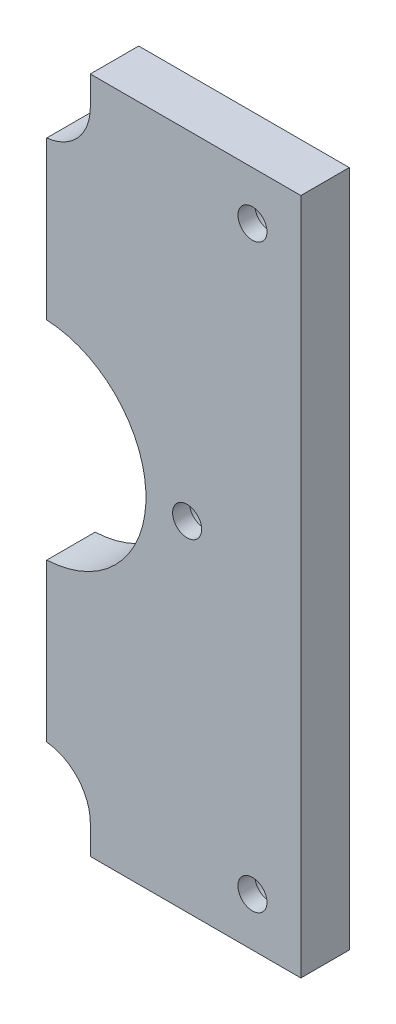
SolidWorks part; units mm, degrees
material "7079 Alloy"
ref_plane "Front" through (0, 0, 0) normal (0, 0, 1) x (1, 0, 0)
ref_plane "Top" through (0, 0, 0) normal (0, 1, 0) x (1, 0, 0)
ref_plane "Right" through (0, 0, 0) normal (1, 0, 0) x (0, 0, -1)
sketch "Sketch1" plane through (0, 0, 0) normal (0, 0, 1) x (1, 0, 0)
  line L0 (26.5, 140) -> (20.5, 140)
  line L1 (20.5, 0) -> (26.5, 0)
  line L2 (5.5, 100) -> (20.5, 100)
  line L3 (26.5, 6) -> (26.5, 0)
  line L4 (90, 0) -> (90, 140)
  line L5 (5.5, 40) -> (20.5, 40)
  line L6 (37.4999, 100) -> (37.4999, 91.4767)
  line L7 (26.5, 140) -> (26.5, 134)
  line L8 (35.5, 100) -> (35.5, 91.4767)
  line L9 (5.5, 100) -> (0, 100)
  line L10 (35.5, 40) -> (35.5, 48.5233)
  line L11 (20.5, 40) -> (20.5, 0)
  line L12 (20.5, 100) -> (20.5, 140)
  line L13 (0, 140) -> (0, 0) construction
  line L14 (37.4999, 48.5233) -> (37.4999, 39.9891)
  line L15 (46.5, 0) -> (46.5, 6)
  line L16 (46.5, 140) -> (90, 140)
  line L17 (37.4999, 15.9499) -> (37.4999, 39.9891)
  line L18 (46.5, 140) -> (46.5, 134)
  line L19 (37.4999, 100) -> (37.4999, 124.0501)
  line L20 (0, 140) -> (26.5, 140) construction
  line L21 (46.5, 0) -> (90, 0)
  line L22 (0, 100) -> (0, 40)
  line L23 (35.5, 124.0501) -> (35.5, 100)
  line L24 (35.5, 40) -> (35.5, 15.9499)
  line L25 (0, 40) -> (5.5, 40)
  arc A0 (35.5, 91.4767) -> (35.5, 48.5233) centre (36.5, 70) ccw
  circle A1 centre (80, 10) radius 3
  circle A2 centre (66.5, 70) radius 3
  circle A3 centre (80, 130) radius 3
  arc A4 (37.4999, 48.5233) -> (37.4999, 91.4767) centre (36.5, 70) ccw
  arc A5 (35.5, 15.9499) -> (26.5, 6) centre (36.5, 6) ccw
  arc A6 (26.5, 134) -> (46.5, 134) centre (36.5, 134) ccw
  arc A7 (46.5, 6) -> (37.4999, 15.9499) centre (36.5, 6) ccw
  circle A8 centre (6.5, 70) radius 3
  dimension "D1" = 140
extrude "Extrude2" add sketch "Sketch1" along normal blind 10
sketch "Sketch5" plane through (0, 0, 0) normal (0, 0, -1) x (-1, 0, 0)
  circle A0 centre (-66.5, 70) radius 5
  circle A1 centre (-80, 10) radius 5
  circle A2 centre (-80, 130) radius 5
extrude "Cut-Extrude2" cut sketch "Sketch5" against normal blind 6.5
sketch "Sketch7" plane through (37.4999, 0, 0) normal (-1, 0, 0) x (0, 0, 1)
  circle A0 centre (5, 110) radius 2.25
  circle A1 centre (5, 30) radius 2.25
extrude "Cut-Extrude3" cut sketch "Sketch7" against normal blind 20
sketch "Sketch8" plane through (37.4999, 0, 0) normal (-1, 0, 0) x (0, 0, 1)
  line L0 (5, 91.4767) -> (5, 98.9767)
  line L1 (10, 91.4767) -> (0, 91.4767) construction
  line L2 (5, 48.5233) -> (5, 41.0233)
  line L3 (10, 48.5233) -> (0, 48.5233) construction
  circle A0 centre (5, 41.0233) radius 4
  circle A1 centre (5, 98.9767) radius 4
extrude "Cut-Extrude4" cut sketch "Sketch8" against normal blind 10 contours A1 | A0
